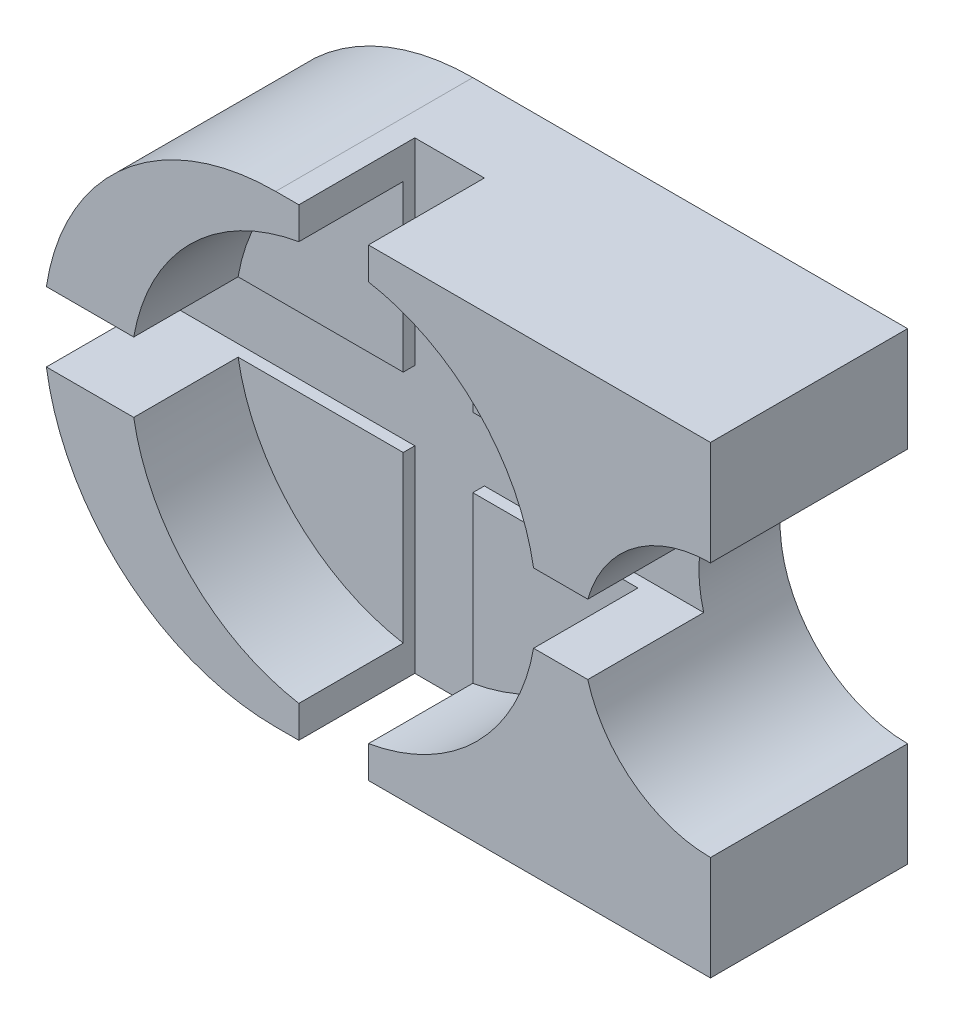
SolidWorks part; units mm, degrees
ref_plane "Front Plane" through (0, 0, 0) normal (0, 0, 1) x (1, 0, 0)
ref_plane "Top Plane" through (0, 0, 0) normal (0, 1, 0) x (1, 0, 0)
ref_plane "Right Plane" through (0, 0, 0) normal (1, 0, 0) x (0, 0, -1)
sketch "Sketch1" plane through (0, 0, 0) normal (0, 0, 1) x (1, 0, 0)
  line L1 (0, 40) -> (75, 40)
  line L2 (0, -40) -> (75, -40)
  line L3 (75, 40) -> (75, -40)
  arc A0 (0, 40) -> (0, -40) centre (0, 0) ccw
  circle A2 centre (75, 0) radius 22
  circle A3 centre (9.6753, 0.3247) radius 32.4428
  point P3 (15.8865, 0)
  dimension "D1" = 40
  dimension "D3" = 44
  dimension "D5" = 64.8856
  dimension "D2" = 75
extrude "Boss-Extrude1" add sketch "Sketch1" along normal blind 34 contours A3 | A2 L3 L1 A0 L2 A3
ref_plane "Plane1" through (0, 0, 34) normal (0, 0, 1) x (1, 0, 0)
sketch "Sketch3" plane through (0, 0, 34) normal (0, 0, 1) x (1, 0, 0)
  line L0 (10, -67.9711) -> (10, 80.5363) construction
  line L1 (-53.5932, 0) -> (64.5166, 0) construction
  line L4 (75, 22) -> (75, 40)
  line L5 (75, 40) -> (0, 40)
  line L6 (0, -40) -> (75, -40)
  line L7 (75, -40) -> (75, -22)
  line L8 (75, 22) -> (75, 40)
  line L9 (75, 40) -> (0, 40)
  line L10 (0, -40) -> (75, -40)
  line L11 (75, -40) -> (75, -22)
  circle A0 centre (10, 0) radius 35
  arc A2 (75, 22) -> (75, -22) centre (75, 0) ccw
  arc A3 (0, 40) -> (0, -40) centre (0, 0) ccw
  arc A4 (75, 22) -> (75, -22) centre (75, 0) ccw
  arc A5 (0, 40) -> (0, -40) centre (0, 0) ccw
  dimension "D3" = 70
  dimension "D2" = 10
  dimension "D1" = 0
extrude "Cut-Extrude1" cut sketch "Sketch3" against normal blind 18 contours A0
ref_plane "Plane2" through (0, 0, 34) normal (0, 0, 1) x (1, 0, 0)
sketch "Sketch4" plane through (0, 0, 34) normal (0, 0, 1) x (1, 0, 0)
  line L0 (75, 22) -> (75, 40) construction
  line L1 (75, 40) -> (0, 40) construction
  line L2 (0, -40) -> (75, -40) construction
  line L3 (75, -40) -> (75, -22) construction
  line L4 (75, 22) -> (75, 40)
  line L5 (75, 40) -> (0, 40)
  line L6 (0, -40) -> (75, -40)
  line L7 (75, -40) -> (75, -22)
  line L9 (4, 40) -> (16, 40)
  line L10 (4, 40) -> (4, 6)
  line L11 (4, -40) -> (16, -40)
  line L12 (16, 40) -> (16, 6)
  line L15 (-39.5474, 6) -> (4, 6)
  line L17 (-39.5474, -6) -> (4, -6)
  line L21 (16, -6) -> (53.834, -6)
  line L22 (4, -6) -> (4, -40)
  line L24 (16, -6) -> (16, -40)
  line L28 (16, 6) -> (53.834, 6)
  arc A0 (75, 22) -> (75, -22) centre (75, 0) ccw construction
  arc A1 (0, 40) -> (0, -40) centre (0, 0) ccw construction
  circle A2 centre (10, 0) radius 35 construction
  arc A3 (75, 22) -> (75, -22) centre (75, 0) ccw
  arc A4 (0, 40) -> (0, -40) centre (0, 0) ccw
  arc A5 (16, -34.4819) -> (44.4819, -6) centre (10, 0) ccw
  arc A6 (-24.4819, -6) -> (4, -34.4819) centre (10, 0) ccw
  arc A7 (4, 34.4819) -> (-24.4819, 6) centre (10, 0) ccw
  arc A8 (44.4819, 6) -> (16, 34.4819) centre (10, 0) ccw
  dimension "D1" = 12
extrude "Cut-Extrude2" cut sketch "Sketch4" against normal blind 20 contours L15 A4 L17 L22 L6 L24 L21 A3 L28 L12 L5 L10
equation "\"Rectangles\"=12"
equation "\"D1@Sketch4\"=\"Rectangles\""
